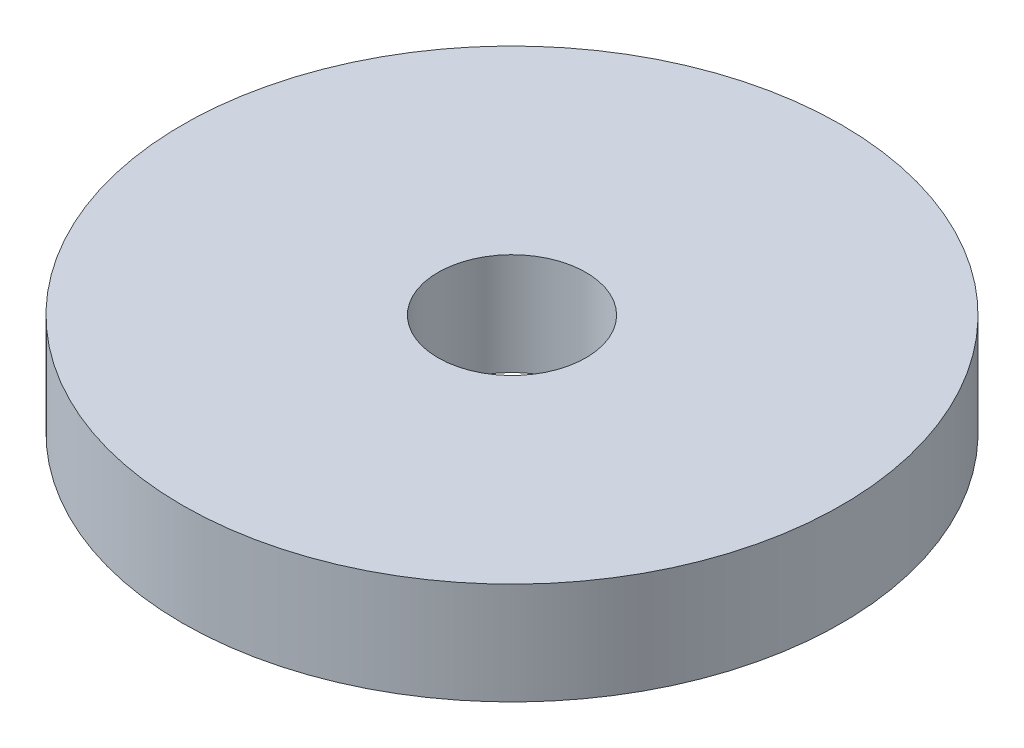
SolidWorks part; units mm, degrees
ref_plane "Front Plane" through (0, 0, 0) normal (0, 0, 1) x (1, 0, 0)
ref_plane "Top Plane" through (0, 0, 0) normal (0, 1, 0) x (1, 0, 0)
ref_plane "Right Plane" through (0, 0, 0) normal (1, 0, 0) x (0, 0, -1)
sketch "Sketch1" plane through (0, 0, 0) normal (0, 1, 0) x (1, 0, 0)
  circle A0 centre (0, 0) radius 22.9704
  circle A1 centre (0, 0) radius 5.1573
extrude "Boss-Extrude1" add sketch "Sketch1" along normal blind 7.112
